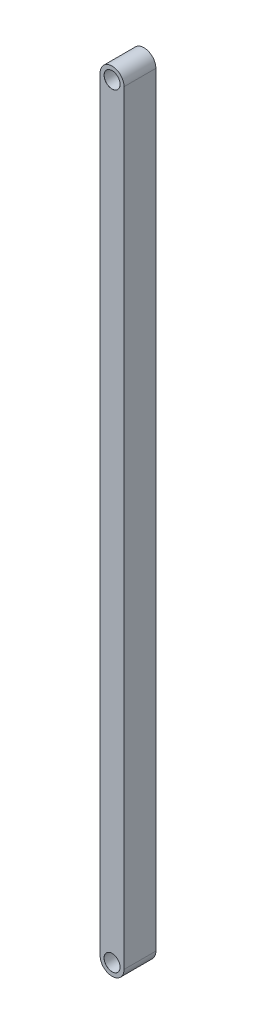
SolidWorks part; units mm, degrees
material "Alloy Steel"
ref_plane "Front Plane" through (0, 0, 0) normal (0, 0, 1) x (1, 0, 0)
ref_plane "Top Plane" through (0, 0, 0) normal (0, 1, 0) x (1, 0, 0)
ref_plane "Right Plane" through (0, 0, 0) normal (1, 0, 0) x (0, 0, -1)
sketch "Sketch2" plane through (0, 0, 0) normal (0, 0, 1) x (1, 0, 0)
  line L0 (-15, -240) -> (-15, 240)
  line L1 (0, 240) -> (0, -240)
  arc A0 (-15, 240) -> (0, 240) centre (-7.5, 240) cw
  arc A1 (0, -240) -> (-15, -240) centre (-7.5, -240) cw
  point P6 (-15, 0)
  dimension "D1" = 480
  dimension "D2" = 15
extrude "Boss-Extrude1" add sketch "Sketch2" along normal blind 20
hole_wizard "Ø10.0mm Dowel Hole1" positions "Sketch3" profile "Sketch4" hole size "Ø10.0" standard "ANSI Metric" end condition through all
sketch "Sketch3" plane through (0, 0, 20) normal (0, 0, 1) x (1, 0, 0)
  point P0 (-7.5, 240)
  point P3 (-7.5, -240)
sketch "Sketch4" plane through (-7.5, 240, 20) normal (1, 0, 0) x (0, -1, 0)
  line L0 (0, 0) -> (0, 20)
  line L1 (0, 20) -> (5, 20)
  line L2 (5, 20) -> (5, 0.025)
  line L3 (5, 0.025) -> (5.025, 0)
  line L5 (5.025, 0) -> (0, 0)
  line L6 (-5, 0.025) -> (-5.025, 0) construction
  line L11 (0, -6.35) -> (0, 107.95) construction
  dimension "Thru Hole Dia." = 10
  dimension "Thru Hole Depth" = 20
  dimension "Near C'Sink Dia." = 10.05
  dimension "Near C'Sink Angle" = 90
